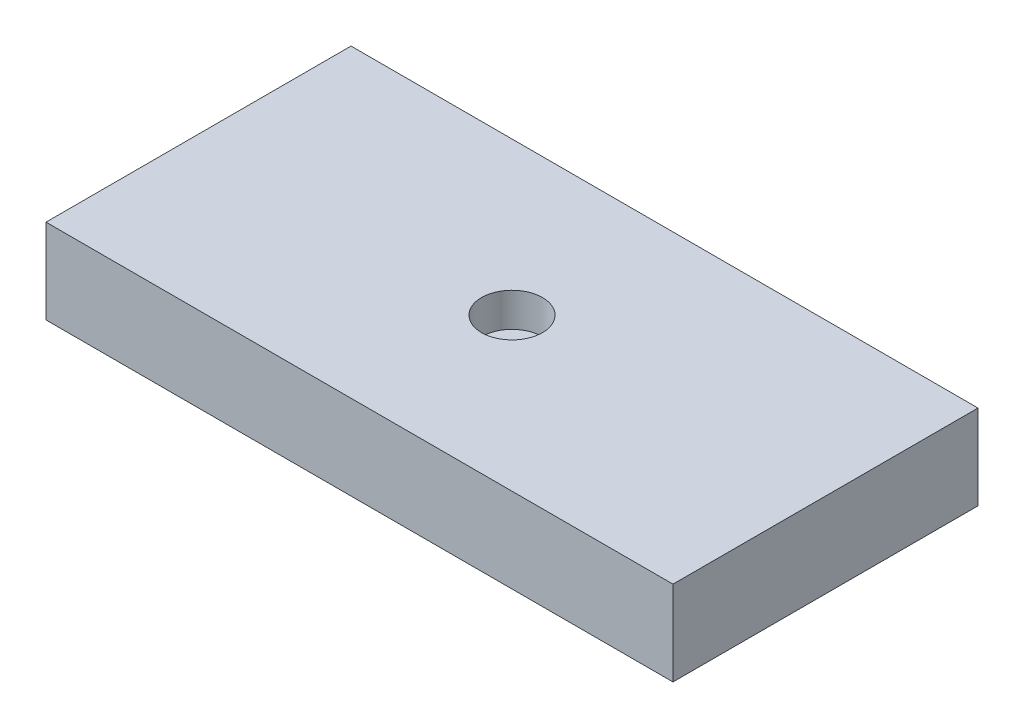
SolidWorks part; units mm, degrees
ref_plane "Front Plane" through (0, 0, 0) normal (0, 0, 1) x (1, 0, 0)
ref_plane "Top Plane" through (0, 0, 0) normal (0, 1, 0) x (1, 0, 0)
ref_plane "Right Plane" through (0, 0, 0) normal (1, 0, 0) x (0, 0, -1)
sketch "Sketch1" plane through (0, 0, 0) normal (0, 1, 0) x (1, 0, 0)
  line L1 (-18.5, -9) -> (18.5, -9)
  line L2 (-18.5, -9) -> (-18.5, 9)
  line L3 (-18.5, 9) -> (18.5, 9)
  line L4 (18.5, -9) -> (18.5, 9)
  line L5 (-18.5, -9) -> (18.5, 9) construction
  line L6 (-18.5, 9) -> (18.5, -9) construction
  point P0 (0, 0)
  dimension "D1" = 37
  dimension "D2" = 18
extrude "Boss-Extrude1" add sketch "Sketch1" along normal blind 5
sketch "Sketch2" plane through (0, 5, 0) normal (0, 1, 0) x (1, 0, 0)
  circle A0 centre (0, 0) radius 1.7968
extrude "Cut-Extrude1" cut sketch "Sketch2" against normal blind 2
